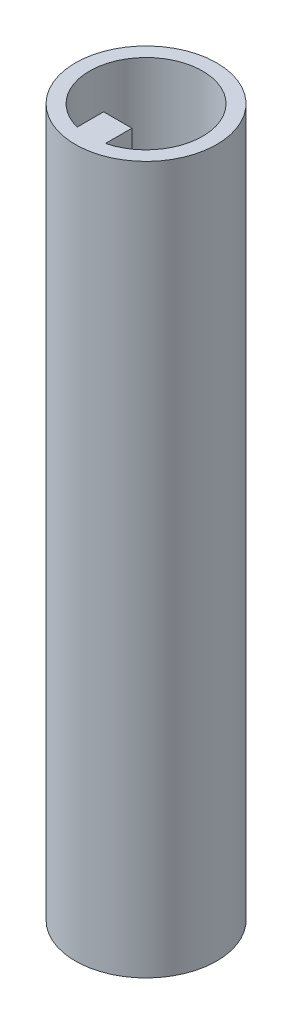
SolidWorks part; units mm, degrees
ref_plane "Alzado" through (0, 0, 0) normal (0, 0, 1) x (1, 0, 0)
ref_plane "Planta" through (0, 0, 0) normal (0, 1, 0) x (1, 0, 0)
ref_plane "Vista lateral" through (0, 0, 0) normal (1, 0, 0) x (0, 0, -1)
sketch "Croquis1" plane through (0, -56.6119, 0) normal (0, -1, 0) x (1, 0, 0)
  line L9 (-1.0394, 38.3655) -> (-1.0394, 34.6195)
  line L10 (-1.0394, 34.6195) -> (-5.0394, 34.6195)
  line L11 (-5.0394, 34.6195) -> (-5.0394, 38.3655)
  line L12 (-1.0394, 38.3655) -> (-1.0394, 34.6195)
  line L13 (-1.0394, 34.6195) -> (-5.0394, 34.6195)
  line L14 (-5.0394, 34.6195) -> (-5.0394, 38.3655)
  circle A4 centre (-3.0394, 30.6195) radius 10
  arc A5 (-5.0394, 38.3655) -> (-1.0394, 38.3655) centre (-3.0394, 30.6195) ccw
  arc A6 (-5.0394, 38.3655) -> (-1.0394, 38.3655) centre (-3.0394, 30.6195) ccw
  dimension "D1" = 0.2
extrude "Saliente-Extruir1" add sketch "Croquis1" along normal blind 100
sketch "Croquis2" plane through (0, -156.6119, 0) normal (0, -1, 0) x (1, 0, 0)
  circle A0 centre (-3.0394, 30.6195) radius 10 construction
  circle A1 centre (-3.0394, 30.6195) radius 10
  circle A2 centre (-3.0394, 30.6195) radius 2.75
  dimension "D1" = 5.5
extrude "Saliente-Extruir2" add sketch "Croquis2" against normal blind 3
sketch "Croquis3" plane through (0, -156.6119, 0) normal (0, -1, 0) x (1, 0, 0)
  circle A0 centre (-3.0394, 37.5774) radius 0.9
  circle A1 centre (3.9185, 30.6195) radius 0.9
  circle A2 centre (-3.0394, 23.6616) radius 0.9
  circle A3 centre (-9.9973, 30.6195) radius 0.9
  point P3 (-3.0394, 30.6195)
  point P13 (-3.0394, 30.6195)
  dimension "D1" = 1.8
  dimension "D2" = 4
extrude "Cortar-Extruir1" cut sketch "Croquis3" against normal blind 10
